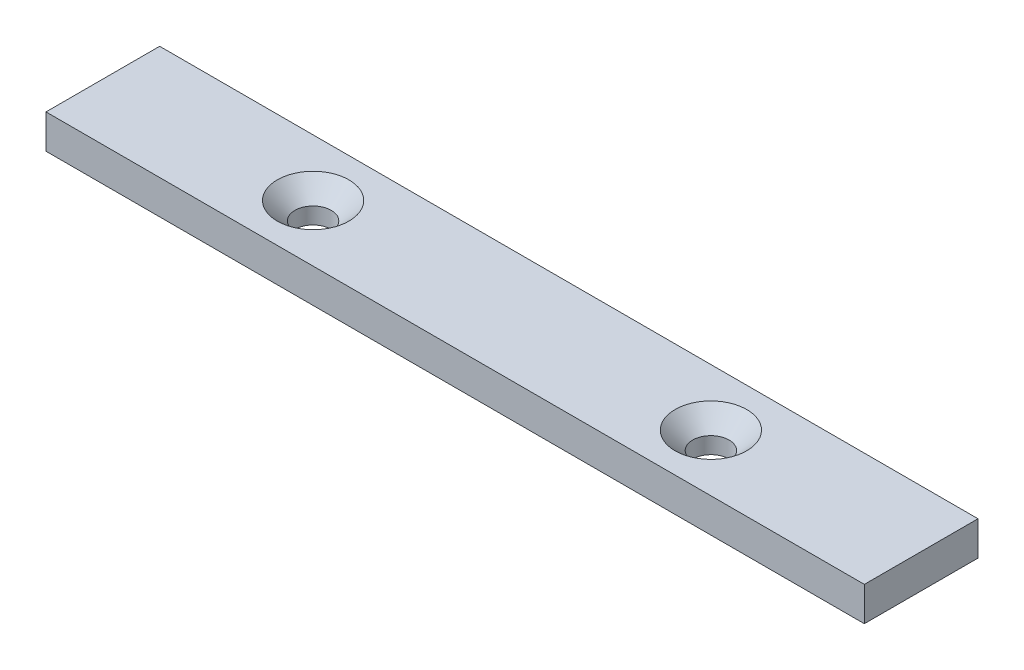
SolidWorks part; units mm, degrees
ref_plane "Front Plane" through (0, 0, 0) normal (0, 0, 1) x (1, 0, 0)
ref_plane "Top Plane" through (0, 0, 0) normal (0, 1, 0) x (1, 0, 0)
ref_plane "Right Plane" through (0, 0, 0) normal (1, 0, 0) x (0, 0, -1)
sketch "Sketch1" plane through (0, 0, 0) normal (0, 1, 0) x (1, 0, 0)
  line L1 (-72, 10) -> (72, 10)
  line L2 (-72, 10) -> (-72, -10)
  line L3 (-72, -10) -> (72, -10)
  line L4 (72, 10) -> (72, -10)
  line L5 (-72, 10) -> (72, -10) construction
  line L6 (-72, -10) -> (72, 10) construction
  point P0 (0, 0)
  dimension "D1" = 144
  dimension "D2" = 20
extrude "Boss-Extrude1" add sketch "Sketch1" along normal blind 6
hole_wizard "Hole1" positions "Sketch2" profile "Sketch3" legacy
sketch "Sketch2" plane through (0, 6, 0) normal (0, 1, 0) x (1, 0, 0)
  line L1 (-72, 10) -> (-72, -10) construction
  point P0 (-35, 0)
  point P2 (35, 0)
  dimension "D1" = 70
  dimension "D2" = 37
sketch "Sketch3" plane through (-35, 6, 0) normal (1, 0, 0) x (0, 0, 1)
  line L0 (0, 0) -> (0, 6)
  line L1 (0, 6) -> (3.2, 6)
  line L2 (3.2, 6) -> (3.2, 3.1)
  line L3 (3.2, 3.1) -> (6.3, 0)
  line L4 (6.3, 0) -> (0, 0)
  line L5 (0, -14.3089) -> (0, 102.4216) construction
  line L6 (0, 6) -> (-3.2, 6) construction
  line L7 (-3.2, 3.1) -> (-6.3, 0) construction
  dimension "Diameter" = 6.4
  dimension "Depth" = 6
  dimension "C-Sink Diameter" = 12.6
  dimension "C-Sink Angle" = 90
  dimension "Drill Angle" = 180
